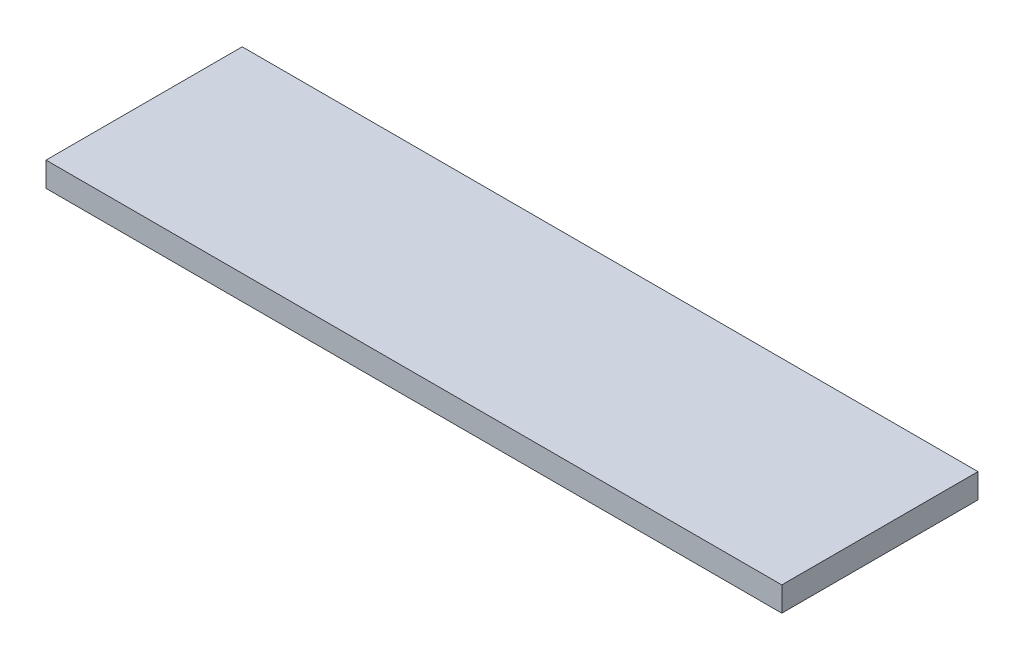
SolidWorks part; units mm, degrees
material "Acrílico (médio-alto impacto)"
ref_plane "Plano frontal" through (0, 0, 0) normal (0, 0, 1) x (1, 0, 0)
ref_plane "Plano superior" through (0, 0, 0) normal (0, 1, 0) x (1, 0, 0)
ref_plane "Plano direito" through (0, 0, 0) normal (1, 0, 0) x (0, 0, -1)
sketch "Esboço7" plane through (0, 0, 0) normal (0, 0, 1) x (1, 0, 0)
  line L1 (83.3573, -431.3355) -> (-66.6427, -431.3355) construction
  line L2 (108.3573, -406.3355) -> (108.3573, -256.3355) construction
  line L3 (83.3573, -231.3355) -> (-66.6427, -231.3355)
  line L4 (-91.6427, -406.3355) -> (-91.6427, -256.3355) construction
  line L5 (83.3573, -231.3355) -> (-66.6427, -231.3355)
  line L6 (83.3573, -231.3355) -> (83.3573, -236.3355)
  line L7 (83.3573, -236.3355) -> (-66.6427, -236.3355)
  line L8 (-66.6427, -231.3355) -> (-66.6427, -236.3355)
  line L9 (108.3573, -406.3355) -> (103.3573, -406.3355) construction
  line L10 (108.3573, -406.3355) -> (108.3573, -256.3355) construction
  line L11 (108.3573, -256.3355) -> (103.3573, -256.3355) construction
  line L12 (103.3573, -406.3355) -> (103.3573, -256.3355) construction
  line L13 (83.3573, -431.3355) -> (-66.6427, -431.3355) construction
  line L14 (83.3573, -431.3355) -> (83.3573, -426.3355) construction
  line L15 (83.3573, -426.3355) -> (-66.6427, -426.3355) construction
  line L16 (-66.6427, -431.3355) -> (-66.6427, -426.3355) construction
  line L17 (-91.6427, -406.3355) -> (-86.6427, -406.3355) construction
  line L18 (-91.6427, -406.3355) -> (-91.6427, -256.3355) construction
  line L19 (-91.6427, -256.3355) -> (-86.6427, -256.3355) construction
  line L20 (-86.6427, -406.3355) -> (-86.6427, -256.3355) construction
  arc A0 (-66.6427, -231.3355) -> (-91.6427, -256.3355) centre (-66.6427, -256.3355) ccw construction
  arc A1 (-66.6427, -431.3355) -> (-91.6427, -406.3355) centre (-66.6427, -406.3355) cw construction
  arc A2 (83.3573, -431.3355) -> (108.3573, -406.3355) centre (83.3573, -406.3355) ccw construction
  arc A3 (108.3573, -256.3355) -> (83.3573, -231.3355) centre (83.3573, -256.3355) ccw construction
  point P6 (-91.6427, -231.3355)
  point P11 (108.3573, -431.3355)
  point P14 (108.3573, -231.3355)
  dimension "D3" = 25
  dimension "D1" = 200
  dimension "D2" = 200
  dimension "D4" = 5
  dimension "D5" = 5
  dimension "D6" = 5
  dimension "D7" = 5
  dimension "D8" = 150
extrude "Ressalto-extrusão2" add sketch "Esboço7" along normal blind 40 contours L3 L8 L7 L6
